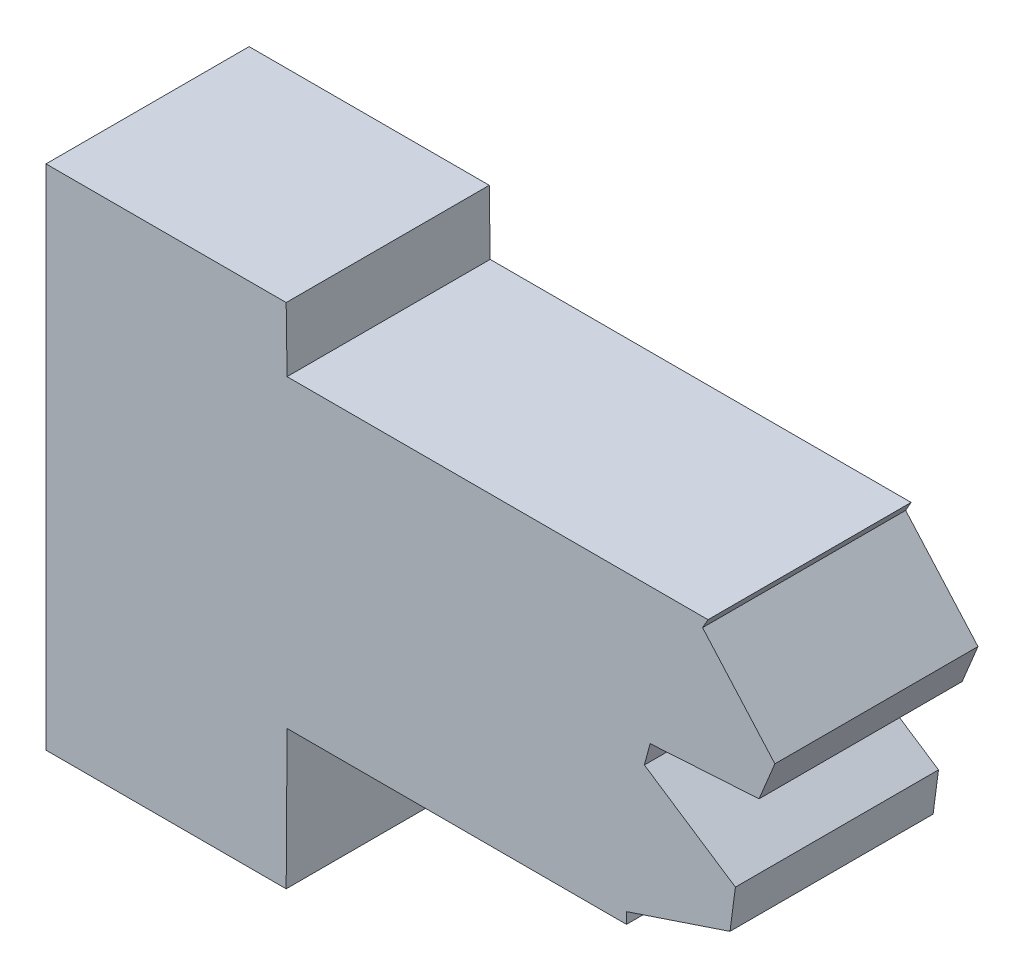
SolidWorks part; units mm, degrees
ref_plane "Front Plane" through (0, 0, 0) normal (0, 0, 1) x (1, 0, 0)
ref_plane "Top Plane" through (0, 0, 0) normal (0, 1, 0) x (1, 0, 0)
ref_plane "Right Plane" through (0, 0, 0) normal (1, 0, 0) x (0, 0, -1)
sketch "Sketch1" plane through (0, 0, 0) normal (0, 0, 1) x (1, 0, 0)
  line L0 (4.7478, 2.7448) -> (11.4321, 2.7448)
  line L1 (4.7478, 2.7448) -> (4.73, 0)
  line L2 (4.7478, 8.7448) -> (13.0378, 8.7448)
  line L3 (11.4321, 2.7448) -> (11.4321, 2.9629)
  line L4 (4.73, 0) -> (0, 0)
  line L5 (11.4321, 2.9629) -> (13.4707, 3.6448)
  line L6 (13.4707, 3.6448) -> (13.5771, 4.4531)
  line L7 (13.5771, 4.4531) -> (11.7845, 5.6394)
  line L8 (11.7845, 5.6394) -> (11.8973, 6.0607)
  line L9 (11.8973, 6.0607) -> (14.043, 6.1918)
  line L10 (14.043, 6.1918) -> (14.355, 6.9451)
  line L11 (14.355, 6.9451) -> (12.9305, 8.5549)
  line L12 (12.9305, 8.5549) -> (13.0378, 8.7448)
  line L13 (4.73, 10) -> (0, 10)
  line L14 (0, 0) -> (0, 10)
  line L15 (4.73, 10) -> (4.7478, 8.7448)
  dimension "D1" = 4.73
  dimension "D2" = 4.7478
  dimension "D23" = 10
  dimension "D13" = 2.7448
  dimension "D3" = 1.2552
  dimension "D4" = 8.29
  dimension "D5" = 0.4362
  dimension "D6" = 2.1496
  dimension "D7" = 0.8153
  dimension "D8" = 0.2181
  dimension "D9" = 8.5549
  dimension "D10" = 6.9451
  dimension "D11" = 6.1918
  dimension "D12" = 6.0607
  dimension "D14" = 5.6394
  dimension "D15" = 4.4531
  dimension "D16" = 3.6448
extrude "Boss-Extrude1" add sketch "Sketch1" along normal blind 4
equation "\"D4@Sketch1\" = \"ThumbLinkLengthMCP@Sketch1@thumbMovingBracketDown<1>.Part@thumbMovingMechanism<2>.Assembly@thumbMechanismAssembly<1>.Assembly\" - 10.7'Toothed Mechanism"
